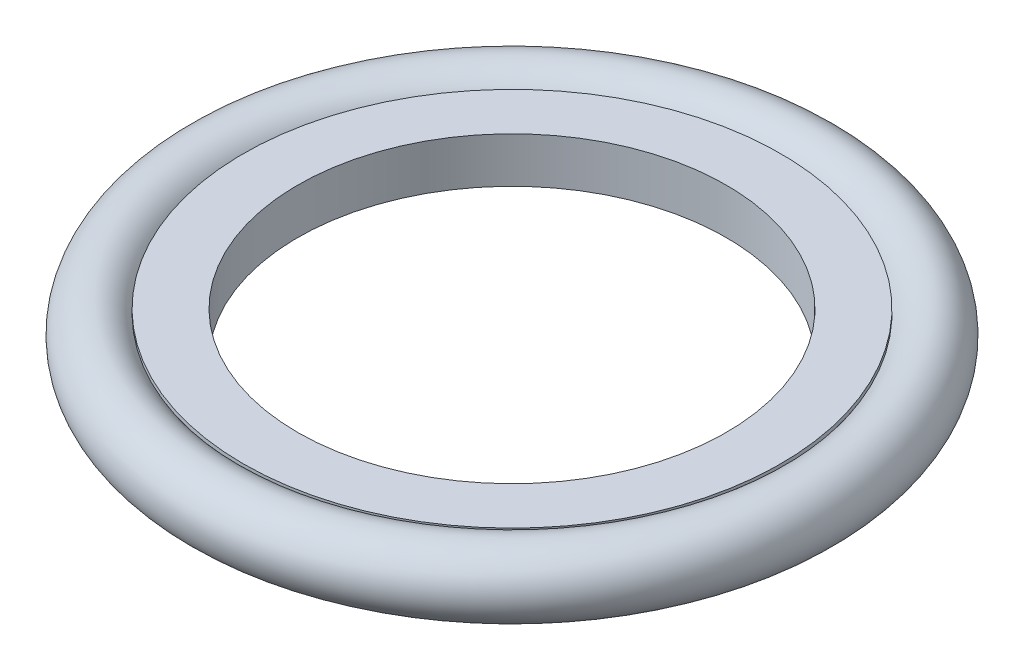
SolidWorks part; units mm, degrees
ref_plane "Front Plane" through (0, 0, 0) normal (0, 0, 1) x (1, 0, 0)
ref_plane "Top Plane" through (0, 0, 0) normal (0, 1, 0) x (1, 0, 0)
ref_plane "Right Plane" through (0, 0, 0) normal (1, 0, 0) x (0, 0, -1)
sketch "Sketch2" plane through (0, 0, 0) normal (1, 0, 0) x (0, 0, -1)
  line L0 (0, 0) -> (209.55, 0) construction
  line L1 (139.7, 0) -> (-139.7, 0) construction
  line L2 (209.55, 0) -> (254, 0) construction
  line L3 (209.55, 17.4625) -> (209.55, -17.4625) construction
  line L4 (0, 0) -> (0, -50000) construction
  circle A0 centre (228.3449, 0) radius 25.6551
  point P8 (209.55, 0)
  dimension "D4" = 51.3103
  dimension "D1" = 209.55
  dimension "D2" = 254
  dimension "D3" = 34.925
revolve "Revolve2" add sketch "Sketch2" angle 360 about L4
sketch "Sketch3" plane through (0, 0, 0) normal (1, 0, 0) x (0, 0, -1)
  line L0 (228.3449, 0) -> (50228.3449, 0) construction
  line L9 (209.6092, 17.526) -> (209.6092, -17.526) construction
  line L10 (207.0791, 17.526) -> (207.0791, 14.351)
  line L11 (207.0791, 14.351) -> (168.3342, 14.351)
  line L12 (168.3342, 14.351) -> (168.3342, -14.351)
  line L13 (207.0791, 17.526) -> (165.1592, 17.526)
  line L14 (165.1592, 17.526) -> (165.1592, -17.526)
  line L15 (207.0791, -17.526) -> (165.1592, -17.526)
  line L16 (207.0791, -14.351) -> (168.3342, -14.351)
  line L17 (207.0791, -17.526) -> (207.0791, -14.351)
  line L18 (0, 0) -> (0, -50000) construction
  circle A1 centre (228.3449, 0) radius 25.6551
  circle A2 centre (228.3449, 0) radius 25.6551 construction
  point P16 (165.1592, 0)
  point P18 (168.3342, 0)
  dimension "D2" = 35.052
  dimension "D3" = 3.175
  dimension "D4" = 3.175
  dimension "D5" = 44.45
  dimension "D1" = 0
revolve "Revolve3" add sketch "Sketch3" angle 360 about L18
